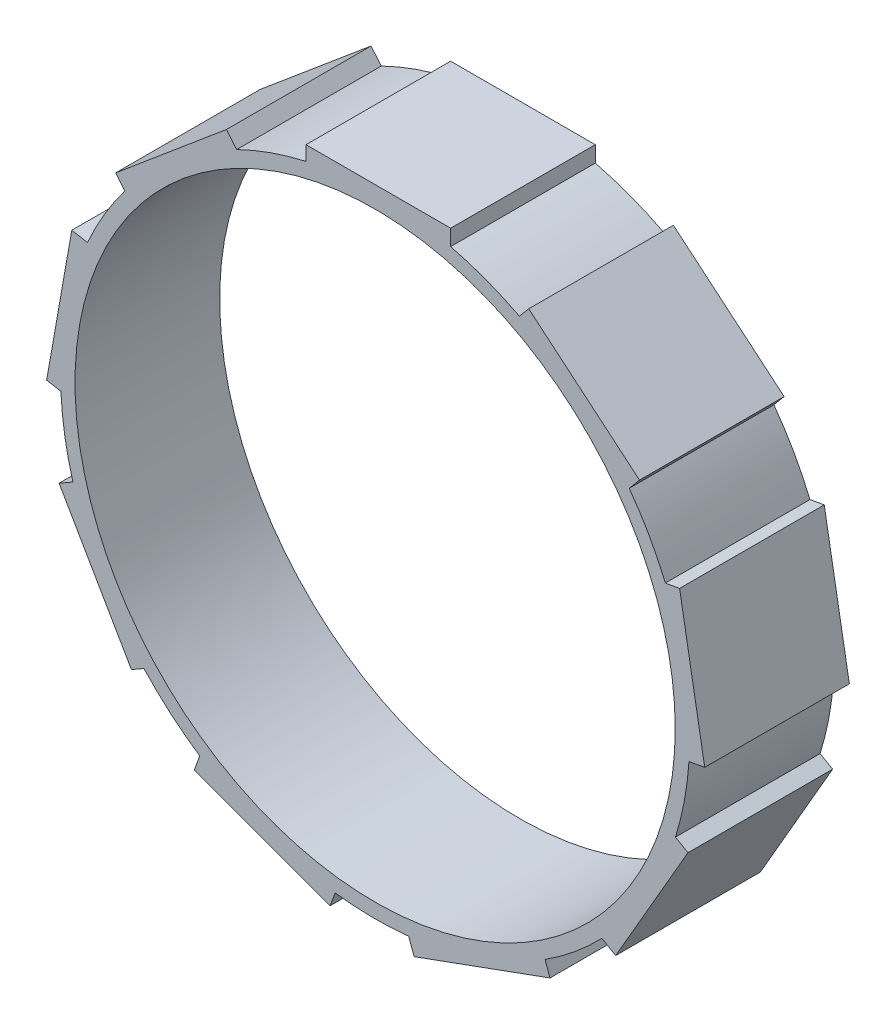
SolidWorks part; units mm, degrees
ref_plane "Alzado" through (0, 0, 0) normal (0, 0, 1) x (1, 0, 0)
ref_plane "Planta" through (0, 0, 0) normal (0, 1, 0) x (1, 0, 0)
ref_plane "Vista lateral" through (0, 0, 0) normal (1, 0, 0) x (0, 0, -1)
sketch "Croquis1" plane through (0, 0, 0) normal (0, 0, 1) x (1, 0, 0)
  line L0 (10.6197, 20.0928) -> (18.2802, 13.6649)
  line L1 (-4.7802, 22.2182) -> (5.2198, 22.2182)
  line L2 (-4.7802, 22.2182) -> (-4.7802, 21.2182)
  line L4 (5.2198, 22.2182) -> (5.2198, 21.1144)
  line L5 (-4.7802, 22.2182) -> (5.8423, 21.1778) construction
  line L6 (-5.6138, 21.2465) -> (5.2198, 22.2182) construction
  line L7 (10.6197, 20.0928) -> (9.9769, 19.3268)
  line L8 (18.2802, 13.6649) -> (17.5706, 12.8193)
  line L9 (21.0506, 8.5657) -> (22.7871, -1.2823)
  line L10 (21.0506, 8.5657) -> (20.0658, 8.3921)
  line L11 (22.7871, -1.2823) -> (21.7, -1.474)
  line L12 (21.6316, -6.9693) -> (16.6316, -15.6296)
  line L13 (21.6316, -6.9693) -> (20.7656, -6.4693)
  line L14 (16.6316, -15.6296) -> (15.6757, -15.0776)
  line L15 (12.091, -19.2433) -> (2.6941, -22.6635)
  line L16 (12.091, -19.2433) -> (11.749, -18.3037)
  line L17 (2.6941, -22.6635) -> (2.3165, -21.6263)
  line L18 (-3.1071, -22.5132) -> (-12.5041, -19.093)
  line L19 (-3.1071, -22.5132) -> (-2.7651, -21.5735)
  line L20 (-12.5041, -19.093) -> (-12.1265, -18.0557)
  line L21 (-16.8514, -15.2489) -> (-21.8514, -6.5886)
  line L22 (-16.8514, -15.2489) -> (-15.9854, -14.7489)
  line L23 (-21.8514, -6.5886) -> (-20.8955, -6.0367)
  line L24 (-22.7107, -0.8494) -> (-20.9743, 8.9986)
  line L25 (-22.7107, -0.8494) -> (-21.7259, -1.0231)
  line L26 (-20.9743, 8.9986) -> (-19.8872, 8.807)
  line L27 (-17.9434, 13.9475) -> (-10.283, 20.3753)
  line L28 (-17.9434, 13.9475) -> (-17.3007, 13.1814)
  line L29 (-10.283, 20.3753) -> (-9.5735, 19.5298)
  circle A0 centre (0, 0) radius 20.75
  arc A1 (-4.7802, 21.2182) -> (5.2198, 21.1144) centre (0, 0) ccw
  point P4 (0, 21.75)
  point P45 (0, 0)
  dimension "D1" = 41.5
  dimension "D2" = 1
  dimension "D3" = 10
  dimension "D5" = 1
  dimension "D4" = 9
extrude "Saliente-Extruir1" add sketch "Croquis1" along normal blind 10 contours A1 L4 L1 L2 A0 | A1 L29 L27 L28 | A1 L8 L0 L7 | A1 L26 L24 L25 | A1 L11 L9 L10 | A1 L14 L12 L13 | A1 L23 L21 L22 | A1 L20 L18 L19 | A1 L17 L15 L16
